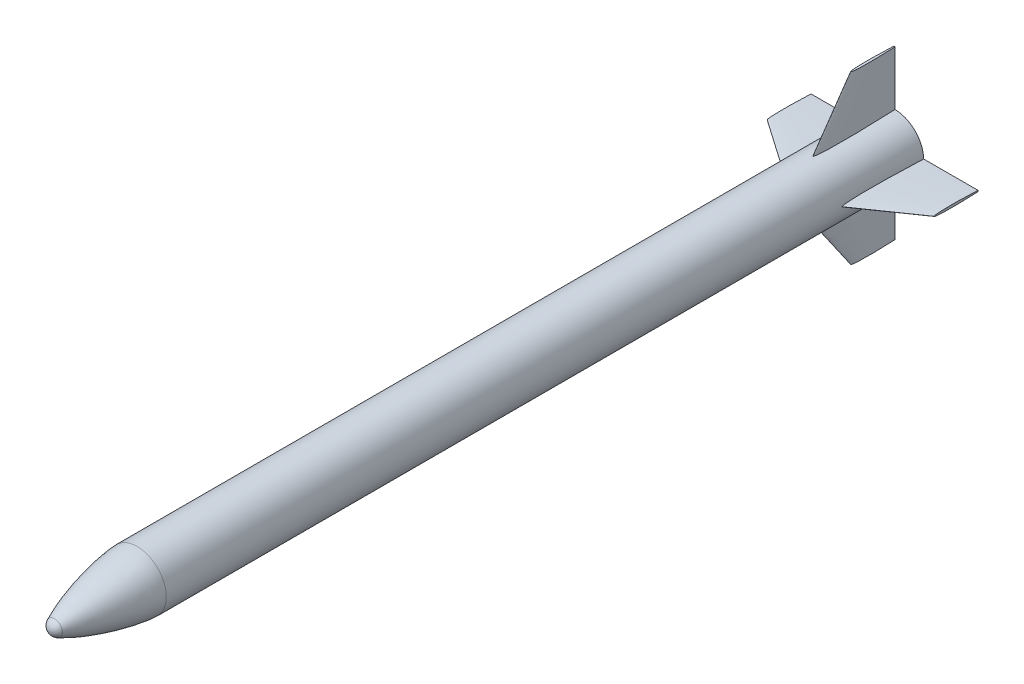
SolidWorks part; units mm, degrees
ref_plane "Front Plane" through (0, 0, 0) normal (0, 0, 1) x (1, 0, 0)
ref_plane "Top Plane" through (0, 0, 0) normal (0, 1, 0) x (1, 0, 0)
ref_plane "Right Plane" through (0, 0, 0) normal (1, 0, 0) x (0, 0, -1)
sketch "Sketch2" plane through (0, 0, 0) normal (1, 0, 0) x (0, 0, -1)
  line L0 (253.9997, 78.3231) -> (2289.4922, 78.3231)
  line L1 (2289.4922, 78.3231) -> (2289.4922, 0.0001)
  line L2 (2289.4922, 0.0001) -> (18.7228, 0.0001)
  line L3 (0, 0) -> (-254, 0) construction
  line L4 (0, 0) -> (0, 78.3229) construction
  arc A0 (32.0138, 21.1648) -> (18.7228, 0.0001) centre (42.2196, 0.0001) ccw
  spline S0 degree 4 poles (11.813, 10.1478) (12.2487, 10.4256) (13.1181, 10.9737) (14.5535, 11.8548) (16.5432, 13.0354) (18.7478, 14.2965) (21.1115, 15.6055) (23.4208, 16.8401) (25.5192, 17.9354) (27.5955, 18.9897) (29.1975, 19.7931) (31.259, 20.8017) (32.5701, 21.4344) (34.4599, 22.3342) (35.9202, 23.0168) (37.9608, 23.9612) (40.3096, 25.027) (43.1983, 26.3124) (46.5377, 27.7606) (49.9116, 29.1898) (53.2841, 30.5849) (57.4082, 32.2551) (62.2796, 34.1747) (67.9903, 36.3539) (73.7249, 38.4627) (78.6581, 40.2244) (83.6033, 41.9499) (88.5609, 43.6407) (94.3612, 45.5641) (101.0113, 47.6975) (107.6811, 49.768) (114.3697, 51.7773) (121.076, 53.7267) (129.4799, 56.0897) (139.5969, 58.8085) (151.4445, 61.8114) (165.0417, 65.0091) (178.6936, 67.9656) (192.3981, 70.6675) (206.1544, 73.0935) (218.3063, 74.9555) (228.7653, 76.3201) (237.4007, 77.2551) (243.1068, 77.7606) (247.5421, 78.0687) (250.508, 78.221) (252.1157, 78.2841) (253.1899, 78.3135) (253.7297, 78.3212) (253.9997, 78.3231) knots 0 0 0 0 0 0.008139 0.016277 0.026477 0.036676 0.04799 0.059304 0.067191 0.075077 0.082963 0.090849 0.097739 0.104629 0.111518 0.118408 0.132187 0.145967 0.161033 0.1761 0.189879 0.203659 0.231217 0.258776 0.286335 0.300114 0.313894 0.341452 0.369011 0.39657 0.424128 0.451687 0.479246 0.506804 0.561922 0.617039 0.672156 0.727274 0.782391 0.837509 0.892626 0.921305 0.948864 0.974603 0.98304 0.991477 0.995739 1 1 1 1 1 construction
  spline S1 degree 4 poles (32.0138, 21.1648) (32.3713, 21.3372) (33.092, 21.6829) (34.4599, 22.3342) (35.9202, 23.0168) (37.9608, 23.9612) (40.3096, 25.027) (43.1983, 26.3124) (46.5377, 27.7606) (49.9116, 29.1898) (53.2841, 30.5849) (57.4082, 32.2551) (62.2796, 34.1747) (67.9903, 36.3539) (73.7249, 38.4627) (78.6581, 40.2244) (83.6033, 41.9499) (88.5609, 43.6407) (94.3612, 45.5641) (101.0113, 47.6975) (107.6811, 49.768) (114.3697, 51.7773) (121.076, 53.7267) (129.4799, 56.0897) (139.5969, 58.8085) (151.4445, 61.8114) (165.0417, 65.0091) (178.6936, 67.9656) (192.3981, 70.6675) (206.1544, 73.0935) (218.3063, 74.9555) (228.7653, 76.3201) (237.4007, 77.2551) (243.1068, 77.7606) (247.5421, 78.0687) (250.508, 78.221) (252.1157, 78.2841) (253.1899, 78.3135) (253.7297, 78.3212) (253.9997, 78.3231) knots 0.090849 0.090849 0.090849 0.090849 0.090849 0.097739 0.104629 0.111518 0.118408 0.132187 0.145967 0.161033 0.1761 0.189879 0.203659 0.231217 0.258776 0.286335 0.300114 0.313894 0.341452 0.369011 0.39657 0.424128 0.451687 0.479246 0.506804 0.561922 0.617039 0.672156 0.727274 0.782391 0.837509 0.892626 0.921305 0.948864 0.974603 0.98304 0.991477 0.995739 1 1 1 1 1
  dimension "D5" = 23.4969
  dimension "D1" = 2035.4925
  dimension "D2" = 254
  dimension "D3" = 78.3229
  dimension "D4" = 78.3229
revolve "Revolve1" add sketch "Sketch2" angle 360 about L2
sketch "Sketch3" plane through (0, 0, -2289.4922) normal (0, 0, -1) x (-1, 0, 0)
  circle A0 centre (0, 0) radius 43.942
  dimension "D1" = 87.884
extrude "Boss-Extrude1" add sketch "Sketch3" along normal blind 15.24
ref_plane "Plane1" through (0, 254, 0) normal (0, 1, 0) x (1, 0, 0)
sketch "Sketch4" plane through (0, 254, 0) normal (0, 1, 0) x (1, 0, 0)
  line L1 (-1.5875, 2083.1172) -> (1.5875, 2083.1172)
  line L2 (-1.5875, 2083.1172) -> (-1.5875, 2286.3172)
  line L3 (-1.5875, 2286.3172) -> (1.5875, 2286.3172)
  line L4 (1.5875, 2083.1172) -> (1.5875, 2286.3172)
  line L5 (78.3229, 2289.4922) -> (-78.3229, 2289.4922) construction
  point P6 (0, 2286.3172)
  dimension "D1" = 3.175
  dimension "D2" = 3.175
  dimension "D3" = 203.2
extrude "Boss-Extrude2" add sketch "Sketch4" against normal up to surface (175.693 mm away)
sketch "Sketch5" plane through (-1.5875, 0, 0) normal (-1, 0, 0) x (0, 0, 1)
  line L0 (-2286.3172, 224.357) -> (-2184.7172, 224.357)
  line L1 (-2286.3172, 78.307) -> (-2286.3172, 254) construction
  line L2 (-2184.7172, 224.357) -> (-2083.1172, 78.307)
  line L3 (-2083.1172, 78.307) -> (-2083.1172, 254)
  line L4 (-2083.1172, 254) -> (-2286.3172, 254)
  line L5 (-2286.3172, 254) -> (-2286.3172, 224.357)
  dimension "D1" = 101.6
  dimension "D2" = 146.05
extrude "Cut-Extrude1" cut sketch "Sketch5" against normal up to next (3.175 mm away)
sketch "Sketch6" plane through (0, 224.357, 0) normal (0, 1, 0) x (1, 0, 0)
  line L0 (0, 2324.1) -> (0, 2171.7) construction
  spline S0 degree 4 poles (0, 2171.7) (0.051, 2171.7006) (0.1231, 2171.7139) (0.2087, 2171.7542) (0.3062, 2171.8284) (0.3808, 2171.9014) (0.4592, 2171.9956) (0.5527, 2172.1319) (0.6711, 2172.3415) (0.8367, 2172.7057) (1.0914, 2173.434) (1.3865, 2174.6081) (1.6836, 2176.1867) (2.0477, 2178.6899) (2.3957, 2181.9018) (2.8436, 2187.452) (3.2338, 2195.3473) (3.4845, 2204.9737) (3.5657, 2216.3247) (3.4973, 2227.6786) (3.3169, 2239.0263) (3.0506, 2250.3803) (2.7588, 2260.3008) (2.4732, 2268.8226) (2.1645, 2277.3095) (1.8846, 2284.4423) (1.593, 2291.4551) (1.2729, 2298.6554) (1.0213, 2304.1337) (0.7286, 2310.1507) (0.4762, 2315.2186) (0.091, 2322.4894) (-0.1374, 2326.6114) (-0.4882, 2332.7319) (-0.6703, 2335.6828) (-0.8182, 2338.1424) (-0.8568, 2338.7185) (-0.8967, 2339.3772) knots 0 0 0 0 0 0.001189 0.001745 0.002211 0.002902 0.003665 0.004655 0.006135 0.008619 0.013162 0.022972 0.034881 0.04679 0.073274 0.099757 0.167217 0.234678 0.302138 0.369599 0.437059 0.504519 0.57198 0.60571 0.63944 0.7069 0.74063 0.774361 0.808091 0.841821 0.875551 0.909281 0.954641 0.97732 0.98866 1 1 1 1 1 construction
  spline S1 degree 4 poles (0, 2171.7) (0.051, 2171.7006) (0.1231, 2171.7139) (0.2087, 2171.7542) (0.3062, 2171.8284) (0.3808, 2171.9014) (0.4592, 2171.9956) (0.5527, 2172.1319) (0.6711, 2172.3415) (0.8367, 2172.7057) (1.0914, 2173.434) (1.3865, 2174.6081) (1.6836, 2176.1867) (2.0477, 2178.6899) (2.3957, 2181.9018) (2.8436, 2187.452) (3.2338, 2195.3473) (3.4845, 2204.9737) (3.5657, 2216.3247) (3.4973, 2227.6786) (3.3169, 2239.0263) (3.0506, 2250.3803) (2.7588, 2260.3008) (2.4732, 2268.8226) (2.1645, 2277.3095) (1.8846, 2284.4423) (1.593, 2291.4551) (1.2729, 2298.6554) (1.0213, 2304.1337) (0.7286, 2310.1507) (0.4762, 2315.2186) (0.2102, 2320.239) (0.0709, 2322.8117) (0, 2324.1) knots 0 0 0 0 0 0.001189 0.001745 0.002211 0.002902 0.003665 0.004655 0.006135 0.008619 0.013162 0.022972 0.034881 0.04679 0.073274 0.099757 0.167217 0.234678 0.302138 0.369599 0.437059 0.504519 0.57198 0.60571 0.63944 0.7069 0.74063 0.774361 0.808091 0.841821 0.875551 0.909281 0.909281 0.909281 0.909281 0.909281
  spline S2 degree 4 poles (0, 2171.7) (-0.051, 2171.7006) (-0.1231, 2171.7139) (-0.2087, 2171.7542) (-0.3062, 2171.8284) (-0.3808, 2171.9014) (-0.4592, 2171.9956) (-0.5527, 2172.1319) (-0.6711, 2172.3415) (-0.8367, 2172.7057) (-1.0914, 2173.434) (-1.3865, 2174.6081) (-1.6836, 2176.1867) (-2.0477, 2178.6899) (-2.3957, 2181.9018) (-2.8436, 2187.452) (-3.2338, 2195.3473) (-3.4845, 2204.9737) (-3.5657, 2216.3247) (-3.4973, 2227.6786) (-3.3169, 2239.0263) (-3.0506, 2250.3803) (-2.7588, 2260.3008) (-2.4732, 2268.8226) (-2.1645, 2277.3095) (-1.8846, 2284.4423) (-1.593, 2291.4551) (-1.2729, 2298.6554) (-1.0213, 2304.1337) (-0.7286, 2310.1507) (-0.4762, 2315.2186) (-0.2102, 2320.239) (-0.0709, 2322.8117) (0, 2324.1) knots 0 0 0 0 0 0.001189 0.001745 0.002211 0.002902 0.003665 0.004655 0.006135 0.008619 0.013162 0.022972 0.034881 0.04679 0.073274 0.099757 0.167217 0.234678 0.302138 0.369599 0.437059 0.504519 0.57198 0.60571 0.63944 0.7069 0.74063 0.774361 0.808091 0.841821 0.875551 0.909281 0.909281 0.909281 0.909281 0.909281
ref_plane "Plane2" through (0, 78.105, 0) normal (0, 1, 0) x (1, 0, 0)
sketch "Sketch7" plane through (0, 78.105, 0) normal (0, 1, 0) x (1, 0, 0)
  line L0 (0, 2324.1) -> (0, 2070.1) construction
  spline S0 degree 4 poles (0, 2070.1) (0.0342, 2070.1002) (0.1014, 2070.1073) (0.2316, 2070.1502) (0.3603, 2070.247) (0.4625, 2070.3536) (0.562, 2070.481) (0.6446, 2070.6032) (0.7505, 2070.7852) (0.8922, 2071.0745) (1.0839, 2071.5498) (1.3694, 2072.4381) (1.8161, 2074.2937) (2.2988, 2077.1802) (2.77, 2080.9905) (3.2968, 2086.605) (3.7697, 2093.44) (4.2835, 2103.6731) (4.696, 2117.3079) (4.925, 2133.2199) (4.9497, 2151.4074) (4.8018, 2169.593) (4.557, 2185.5057) (4.283, 2199.1414) (3.9649, 2212.7806) (3.6673, 2224.1378) (3.3402, 2235.5096) (2.9883, 2246.8566) (2.6904, 2255.9678) (2.3035, 2267.2859) (1.805, 2280.9991) (1.282, 2294.483) (0.7524, 2307.184) (0.3684, 2315.9782) (0.0635, 2322.737) (-0.1342, 2327.0197) (-0.4722, 2334.1824) (-0.736, 2339.5059) (-1.0136, 2345.0628) (-1.1551, 2347.7422) (-1.2484, 2349.5509) knots 0 0 0 0 0 0.000483 0.000965 0.00193 0.00226 0.00259 0.00327 0.004035 0.005264 0.007185 0.010582 0.017344 0.032491 0.048939 0.065387 0.097843 0.130299 0.19521 0.260121 0.325033 0.389944 0.454856 0.487311 0.519767 0.584679 0.617134 0.64959 0.682046 0.714502 0.779413 0.844324 0.87678 0.893008 0.909236 0.931927 0.954618 0.977309 1 1 1 1 1 construction
  spline S1 degree 4 poles (0, 2070.1) (0.0342, 2070.1002) (0.1014, 2070.1073) (0.2316, 2070.1502) (0.3603, 2070.247) (0.4625, 2070.3536) (0.562, 2070.481) (0.6446, 2070.6032) (0.7505, 2070.7852) (0.8922, 2071.0745) (1.0839, 2071.5498) (1.3694, 2072.4381) (1.8161, 2074.2937) (2.2988, 2077.1802) (2.77, 2080.9905) (3.2968, 2086.605) (3.7697, 2093.44) (4.2835, 2103.6731) (4.696, 2117.3079) (4.925, 2133.2199) (4.9497, 2151.4074) (4.8018, 2169.593) (4.557, 2185.5057) (4.283, 2199.1414) (3.9649, 2212.7806) (3.6673, 2224.1378) (3.3402, 2235.5096) (2.9883, 2246.8566) (2.6904, 2255.9678) (2.3035, 2267.2859) (1.805, 2280.9991) (1.282, 2294.483) (0.7524, 2307.184) (0.3684, 2315.9782) (0.1425, 2320.9863) (0.0475, 2323.0676) (0, 2324.1) knots 0 0 0 0 0 0.000483 0.000965 0.00193 0.00226 0.00259 0.00327 0.004035 0.005264 0.007185 0.010582 0.017344 0.032491 0.048939 0.065387 0.097843 0.130299 0.19521 0.260121 0.325033 0.389944 0.454856 0.487311 0.519767 0.584679 0.617134 0.64959 0.682046 0.714502 0.779413 0.844324 0.87678 0.893008 0.909236 0.909236 0.909236 0.909236 0.909236
  spline S2 degree 4 poles (0, 2070.1) (-0.0342, 2070.1002) (-0.1014, 2070.1073) (-0.2316, 2070.1502) (-0.3603, 2070.247) (-0.4625, 2070.3536) (-0.562, 2070.481) (-0.6446, 2070.6032) (-0.7505, 2070.7852) (-0.8922, 2071.0745) (-1.0839, 2071.5498) (-1.3694, 2072.4381) (-1.8161, 2074.2937) (-2.2988, 2077.1802) (-2.77, 2080.9905) (-3.2968, 2086.605) (-3.7697, 2093.44) (-4.2835, 2103.6731) (-4.696, 2117.3079) (-4.925, 2133.2199) (-4.9497, 2151.4074) (-4.8018, 2169.593) (-4.557, 2185.5057) (-4.283, 2199.1414) (-3.9649, 2212.7806) (-3.6673, 2224.1378) (-3.3402, 2235.5096) (-2.9883, 2246.8566) (-2.6904, 2255.9678) (-2.3035, 2267.2859) (-1.805, 2280.9991) (-1.282, 2294.483) (-0.7524, 2307.184) (-0.3684, 2315.9782) (-0.1425, 2320.9863) (-0.0475, 2323.0676) (0, 2324.1) knots 0 0 0 0 0 0.000483 0.000965 0.00193 0.00226 0.00259 0.00327 0.004035 0.005264 0.007185 0.010582 0.017344 0.032491 0.048939 0.065387 0.097843 0.130299 0.19521 0.260121 0.325033 0.389944 0.454856 0.487311 0.519767 0.584679 0.617134 0.64959 0.682046 0.714502 0.779413 0.844324 0.87678 0.893008 0.909236 0.909236 0.909236 0.909236 0.909236
loft "Loft12" add profiles "Sketch6", "Sketch7"
sketch "Sketch8" plane through (0, 78.105, 0) normal (0, -1, 0) x (1, 0, 0)
  line L0 (-1.4702, -2289.4922) -> (1.4702, -2289.4922) construction
  line L1 (-4.9625, -2289.4922) -> (2.5426, -2289.4922)
  line L2 (-4.9625, -2289.4922) -> (-4.9625, -2339.479)
  line L3 (-4.9625, -2339.479) -> (2.5426, -2339.479)
  line L4 (2.5426, -2289.4922) -> (2.5426, -2339.479)
extrude "Cut-Extrude3" cut sketch "Sketch8" against normal through all
pattern_circular "CirPattern1" count 4 over 360 about axis through (0, 0.0001, -2289.4922) along (0, 0, -1) of "Boss-Extrude2", "Cut-Extrude1", "Loft12", "Cut-Extrude3"
equation "\"Body Tube Length\"= 80.1375"
equation "\"D1@Sketch2\"=\"Body Tube Length\""
equation "\"Retainer Diameter\"= 3.46"
equation "\"D1@Sketch3\"=\"Retainer Diameter\""
equation "\"Retainer Height\"= 0.6"
equation "\"D1@Boss-Extrude1\"=\"Retainer Height\""
equation "\"Fin Offset\"= .125"
equation "\"D1@Sketch4\"=\"Fin Offset\""
equation "\"Fin Thickness\"= .125"
equation "\"D2@Sketch4\"=\"Fin Thickness\""
equation "\"Fin Root Chord\"= 8"
equation "\"D3@Sketch4\"=\"Fin Root Chord\""
equation "\"Fin Tip Chord\"= 4"
equation "\"D1@Sketch5\"=\"Fin Tip Chord\""
equation "\"Fin Height\"= 5.75"
equation "\"D2@Sketch5\"=\"Fin Height\""
equation "\"Fin Epoxy Fillet Radius\"=0.1"
equation "\"Nosecone Length\"= 10"
equation "\"D2@Sketch2\"=\"Nosecone Length\""
equation "\"Rocket Radius\"=3.08358"
equation "\"D3@Sketch2\"= \"Rocket Radius\""
equation "\"D4@Sketch2\"=\"Rocket Radius\""
equation "\"D5@Sketch2\"=\"Rocket Radius\"*2*.15"
